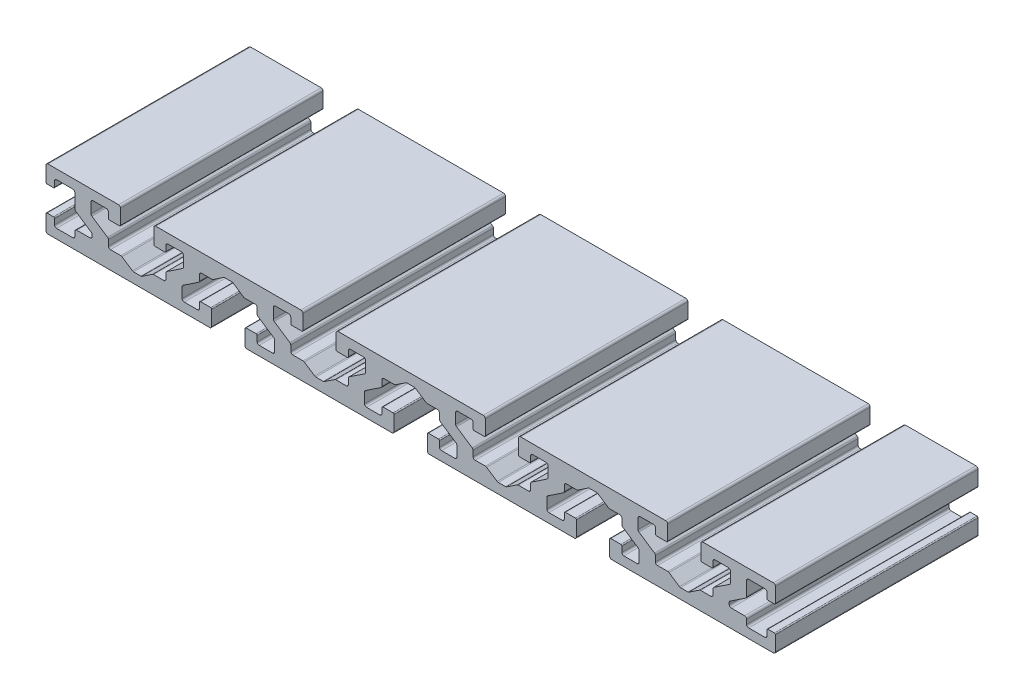
SolidWorks part; units mm, degrees
material "6063-T5"
ref_plane "Front Plane" through (0, 0, 0) normal (0, 0, 1) x (1, 0, 0)
ref_plane "Top Plane" through (0, 0, 0) normal (0, 1, 0) x (1, 0, 0)
ref_plane "Right Plane" through (0, 0, 0) normal (1, 0, 0) x (0, 0, -1)
sketch "Sketch1" plane through (0, 0, 0) normal (0, 0, 1) x (1, 0, 0)
  line L0 (0.5, 0) -> (40.4, 0)
  line L1 (180, 0.5) -> (180, 4.15)
  line L2 (179.5, 15) -> (162.1, 15)
  line L3 (0, 14.5) -> (0, 10.85)
  line L4 (179.75, 4.4) -> (178.15, 4.4)
  line L5 (0.25, 4.4) -> (1.85, 4.4)
  line L6 (179.75, 10.6) -> (178.15, 10.6)
  line L7 (0.25, 10.6) -> (1.85, 10.6)
  line L8 (0, 4.15) -> (0, 0.5)
  line L9 (180, 10.85) -> (180, 14.5)
  line L10 (71.6, 14.5) -> (71.6, 10.85)
  line L11 (18.4, 14.5) -> (18.4, 10.85)
  line L12 (26.6, 14.5) -> (26.6, 10.85)
  line L13 (17.9, 15) -> (0.5, 15)
  line L14 (63.4, 14.5) -> (63.4, 10.85)
  line L15 (116.6, 14.5) -> (116.6, 10.85)
  line L16 (108.4, 14.5) -> (108.4, 10.85)
  line L17 (161.6, 14.5) -> (161.6, 10.85)
  line L18 (153.4, 14.5) -> (153.4, 10.85)
  line L19 (62.9, 15) -> (27.1, 15)
  line L20 (107.9, 15) -> (72.1, 15)
  line L21 (152.9, 15) -> (117.1, 15)
  line L22 (85.9, 0.5) -> (85.9, 4.15)
  line L23 (40.9, 0.5) -> (40.9, 4.15)
  line L24 (49.1, 0.5) -> (49.1, 4.15)
  line L25 (49.6, 0) -> (85.4, 0)
  line L26 (94.1, 0.5) -> (94.1, 4.15)
  line L27 (130.9, 0.5) -> (130.9, 4.15)
  line L28 (139.1, 0.5) -> (139.1, 4.15)
  line L29 (94.6, 0) -> (130.4, 0)
  line L30 (139.6, 0) -> (179.5, 0)
  line L31 (63.15, 10.6) -> (60.65, 10.6)
  line L32 (26.85, 10.6) -> (29.35, 10.6)
  line L33 (18.15, 10.6) -> (15.65, 10.6)
  line L34 (71.85, 10.6) -> (74.35, 10.6)
  line L35 (108.15, 10.6) -> (105.65, 10.6)
  line L36 (116.85, 10.6) -> (119.35, 10.6)
  line L37 (153.15, 10.6) -> (150.65, 10.6)
  line L38 (161.85, 10.6) -> (164.35, 10.6)
  line L39 (40.65, 4.4) -> (38.15, 4.4)
  line L40 (49.35, 4.4) -> (51.85, 4.4)
  line L41 (85.65, 4.4) -> (83.15, 4.4)
  line L42 (94.35, 4.4) -> (96.85, 4.4)
  line L43 (130.65, 4.4) -> (128.15, 4.4)
  line L44 (139.35, 4.4) -> (141.85, 4.4)
  line L45 (52.6, 2.3) -> (55.9, 2.3)
  line L46 (2.6, 2.3) -> (6.6, 2.3)
  line L47 (7.1, 12.2) -> (7.1, 8.7315)
  line L48 (172.9, 12.2) -> (172.9, 8.7315)
  line L49 (6.6, 12.7) -> (2.6, 12.7)
  line L50 (15.4, 10.85) -> (15.4, 12.2)
  line L51 (29.6, 10.85) -> (29.6, 12.2)
  line L52 (74.6, 10.85) -> (74.6, 12.2)
  line L53 (60.4, 10.85) -> (60.4, 12.2)
  line L54 (119.6, 10.85) -> (119.6, 12.2)
  line L55 (105.4, 10.85) -> (105.4, 12.2)
  line L56 (164.6, 10.85) -> (164.6, 12.2)
  line L57 (150.4, 10.85) -> (150.4, 12.2)
  line L58 (37.9, 4.15) -> (37.9, 2.8)
  line L59 (52.1, 4.15) -> (52.1, 2.8)
  line L60 (97.1, 4.15) -> (97.1, 2.8)
  line L61 (82.9, 4.15) -> (82.9, 2.8)
  line L62 (142.1, 4.15) -> (142.1, 2.8)
  line L63 (127.9, 4.15) -> (127.9, 2.8)
  line L64 (56.1, 12.2) -> (56.1, 9.6704)
  line L65 (78.9, 12.2) -> (78.9, 9.6704)
  line L66 (33.9, 12.2) -> (33.9, 9.6704)
  line L67 (30.1, 12.7) -> (33.4, 12.7)
  line L68 (123.6774, 9.2543) -> (119.8226, 6.6845)
  line L69 (21.6056, 2.5) -> (23.3944, 2.5)
  line L70 (11.6, 12.7) -> (14.9, 12.7)
  line L71 (75.1, 12.7) -> (78.4, 12.7)
  line L72 (56.6, 12.7) -> (59.9, 12.7)
  line L73 (120.1, 12.7) -> (123.4, 12.7)
  line L74 (101.6, 12.7) -> (104.9, 12.7)
  line L75 (165.1, 12.7) -> (168.4, 12.7)
  line L76 (146.6, 12.7) -> (149.9, 12.7)
  line L77 (66.6056, 2.5) -> (68.3944, 2.5)
  line L78 (56.3226, 9.2543) -> (60.1774, 6.6845)
  line L79 (101.1, 12.2) -> (101.1, 9.6704)
  line L80 (37.4, 2.3) -> (34.1, 2.3)
  line L81 (97.6, 2.3) -> (100.9, 2.3)
  line L82 (82.4, 2.3) -> (79.1, 2.3)
  line L83 (142.6, 2.3) -> (145.9, 2.3)
  line L84 (127.4, 2.3) -> (124.1, 2.3)
  line L85 (33.6, 2.8) -> (33.6, 5.3296)
  line L86 (56.4, 2.8) -> (56.4, 5.3296)
  line L87 (101.4, 2.8) -> (101.4, 5.3296)
  line L88 (91.1718, 12.416) -> (93.7699, 10.684)
  line L89 (89.1056, 12.5) -> (90.8944, 12.5)
  line L90 (78.8226, 5.7457) -> (82.6774, 8.3155)
  line L91 (168.6774, 9.2543) -> (164.8226, 6.6845)
  line L92 (29.6, 4.9) -> (29.6, 6.2685)
  line L93 (18.4528, 4.4) -> (15.9, 4.4)
  line L94 (26.5472, 4.4) -> (29.1, 4.4)
  line L95 (123.9, 12.2) -> (123.9, 9.6704)
  line L96 (7.3226, 8.3155) -> (11.1774, 5.7457)
  line L97 (15.4, 4.9) -> (15.4, 6.2685)
  line L98 (18.7301, 4.316) -> (21.3282, 2.584)
  line L99 (2.1, 4.15) -> (2.1, 2.8)
  line L100 (2.1, 12.2) -> (2.1, 10.85)
  line L101 (173.4, 12.7) -> (177.4, 12.7)
  line L102 (177.9, 12.2) -> (177.9, 10.85)
  line L103 (173.4, 2.3) -> (177.4, 2.3)
  line L104 (177.9, 2.8) -> (177.9, 4.15)
  line L105 (26.2699, 4.316) -> (23.6718, 2.584)
  line L106 (44.1056, 12.5) -> (45.8944, 12.5)
  line L107 (33.6774, 9.2543) -> (29.8226, 6.6845)
  line L108 (111.6056, 2.5) -> (113.3944, 2.5)
  line L109 (101.3226, 9.2543) -> (105.1774, 6.6845)
  line L110 (146.1, 12.2) -> (146.1, 9.6704)
  line L111 (168.9, 12.2) -> (168.9, 9.6704)
  line L112 (74.6, 4.9) -> (74.6, 6.2685)
  line L113 (156.6056, 2.5) -> (158.3944, 2.5)
  line L114 (97.1, 10.1) -> (97.1, 8.7315)
  line L115 (11.1, 12.2) -> (11.1, 9.6704)
  line L116 (11.3226, 9.2543) -> (15.1774, 6.6845)
  line L117 (146.3226, 9.2543) -> (150.1774, 6.6845)
  line L118 (78.6, 2.8) -> (78.6, 5.3296)
  line L119 (146.4, 2.8) -> (146.4, 5.3296)
  line L120 (33.8226, 5.7457) -> (37.6774, 8.3155)
  line L121 (136.1718, 12.416) -> (138.7699, 10.684)
  line L122 (134.1056, 12.5) -> (135.8944, 12.5)
  line L123 (46.1718, 12.416) -> (48.7699, 10.684)
  line L124 (123.8226, 5.7457) -> (127.6774, 8.3155)
  line L125 (123.6, 2.8) -> (123.6, 5.3296)
  line L126 (78.6774, 9.2543) -> (74.8226, 6.6845)
  line L127 (71.5472, 4.4) -> (74.1, 4.4)
  line L128 (63.4528, 4.4) -> (60.9, 4.4)
  line L129 (60.4, 4.9) -> (60.4, 6.2685)
  line L130 (119.6, 4.9) -> (119.6, 6.2685)
  line L131 (116.5472, 4.4) -> (119.1, 4.4)
  line L132 (108.4528, 4.4) -> (105.9, 4.4)
  line L133 (105.4, 4.9) -> (105.4, 6.2685)
  line L134 (164.6, 4.9) -> (164.6, 6.2685)
  line L135 (161.5472, 4.4) -> (164.1, 4.4)
  line L136 (153.4528, 4.4) -> (150.9, 4.4)
  line L137 (150.4, 4.9) -> (150.4, 6.2685)
  line L138 (63.7301, 4.316) -> (66.3282, 2.584)
  line L139 (71.2699, 4.316) -> (68.6718, 2.584)
  line L140 (108.7301, 4.316) -> (111.3282, 2.584)
  line L141 (116.2699, 4.316) -> (113.6718, 2.584)
  line L142 (153.7301, 4.316) -> (156.3282, 2.584)
  line L143 (161.2699, 4.316) -> (158.6718, 2.584)
  line L144 (11.4, 4.9) -> (11.4, 5.3296)
  line L145 (49.0472, 10.6) -> (51.6, 10.6)
  line L146 (40.9528, 10.6) -> (38.4, 10.6)
  line L147 (37.9, 10.1) -> (37.9, 8.7315)
  line L148 (52.1, 10.1) -> (52.1, 8.7315)
  line L149 (41.2301, 10.684) -> (43.8282, 12.416)
  line L150 (52.3226, 8.3155) -> (56.1774, 5.7457)
  line L151 (94.0472, 10.6) -> (96.6, 10.6)
  line L152 (85.9528, 10.6) -> (83.4, 10.6)
  line L153 (82.9, 10.1) -> (82.9, 8.7315)
  line L154 (142.1, 10.1) -> (142.1, 8.7315)
  line L155 (139.0472, 10.6) -> (141.6, 10.6)
  line L156 (130.9528, 10.6) -> (128.4, 10.6)
  line L157 (127.9, 10.1) -> (127.9, 8.7315)
  line L158 (86.2301, 10.684) -> (88.8282, 12.416)
  line L159 (97.3226, 8.3155) -> (101.1774, 5.7457)
  line L160 (131.2301, 10.684) -> (133.8282, 12.416)
  line L161 (142.3226, 8.3155) -> (146.1774, 5.7457)
  line L162 (7.6, 4.4) -> (10.9, 4.4)
  line L163 (7.1, 3.9) -> (7.1, 2.8)
  line L164 (7.1, 2.3) -> (11.4, 2.3) [skipped]
  line L166 (168.8226, 5.7457) -> (172.6774, 8.3155)
  line L167 (168.6, 4.9) -> (168.6, 5.3296)
  line L170 (172.4, 4.4) -> (169.1, 4.4)
  line L171 (172.9, 3.9) -> (172.9, 2.8)
  line L172 (172.9, 2.3) -> (168.6, 2.3) [skipped]
  line L173 (7.1, 3.9) -> (7.1, 2.3) [skipped]
  line L174 (172.9, 3.9) -> (172.9, 2.3) [skipped]
  arc A0 (0.5, 0) -> (0, 0.5) centre (0.5, 0.5) cw
  arc A1 (0.5, 15) -> (0, 14.5) centre (0.5, 14.5) ccw
  arc A2 (179.5, 0) -> (180, 0.5) centre (179.5, 0.5) ccw
  arc A3 (180, 14.5) -> (179.5, 15) centre (179.5, 14.5) ccw
  arc A4 (161.6, 14.5) -> (162.1, 15) centre (162.1, 14.5) cw
  arc A5 (153.4, 14.5) -> (152.9, 15) centre (152.9, 14.5) ccw
  arc A6 (139.1, 0.5) -> (139.6, 0) centre (139.6, 0.5) ccw
  arc A7 (130.9, 0.5) -> (130.4, 0) centre (130.4, 0.5) cw
  arc A8 (108.4, 14.5) -> (107.9, 15) centre (107.9, 14.5) ccw
  arc A9 (116.6, 14.5) -> (117.1, 15) centre (117.1, 14.5) cw
  arc A10 (85.9, 0.5) -> (85.4, 0) centre (85.4, 0.5) cw
  arc A11 (94.1, 0.5) -> (94.6, 0) centre (94.6, 0.5) ccw
  arc A12 (71.6, 14.5) -> (72.1, 15) centre (72.1, 14.5) cw
  arc A13 (63.4, 14.5) -> (62.9, 15) centre (62.9, 14.5) ccw
  arc A14 (49.6, 0) -> (49.1, 0.5) centre (49.6, 0.5) cw
  arc A15 (40.4, 0) -> (40.9, 0.5) centre (40.4, 0.5) ccw
  arc A16 (17.9, 15) -> (18.4, 14.5) centre (17.9, 14.5) cw
  arc A17 (27.1, 15) -> (26.6, 14.5) centre (27.1, 14.5) ccw
  arc A18 (7.1, 3.9) -> (7.6, 4.4) centre (7.6, 3.9) cw
  arc A19 (10.9, 4.4) -> (11.4, 4.9) centre (10.9, 4.9) ccw
  arc A20 (11.1774, 5.7457) -> (11.4, 5.3296) centre (10.9, 5.3296) cw
  arc A21 (7.3226, 8.3155) -> (7.1, 8.7315) centre (7.6, 8.7315) cw
  arc A22 (2.1, 2.8) -> (2.6, 2.3) centre (2.6, 2.8) ccw
  arc A23 (7.1, 2.8) -> (6.6, 2.3) centre (6.6, 2.8) cw
  arc A24 (7.1, 12.2) -> (6.6, 12.7) centre (6.6, 12.2) ccw
  arc A25 (2.6, 12.7) -> (2.1, 12.2) centre (2.6, 12.2) ccw
  arc A26 (29.6, 12.2) -> (30.1, 12.7) centre (30.1, 12.2) cw
  arc A27 (33.4, 12.7) -> (33.9, 12.2) centre (33.4, 12.2) cw
  arc A28 (33.9, 9.6704) -> (33.6774, 9.2543) centre (33.4, 9.6704) cw
  arc A29 (29.6, 6.2685) -> (29.8226, 6.6845) centre (30.1, 6.2685) cw
  arc A30 (29.1, 4.4) -> (29.6, 4.9) centre (29.1, 4.9) ccw
  arc A31 (26.5472, 4.4) -> (26.2699, 4.316) centre (26.5472, 3.9) ccw
  arc A32 (23.3944, 2.5) -> (23.6718, 2.584) centre (23.3944, 3) ccw
  arc A33 (21.6056, 2.5) -> (21.3282, 2.584) centre (21.6056, 3) cw
  arc A34 (18.4528, 4.4) -> (18.7301, 4.316) centre (18.4528, 3.9) cw
  arc A35 (15.9, 4.4) -> (15.4, 4.9) centre (15.9, 4.9) cw
  arc A36 (15.4, 6.2685) -> (15.1774, 6.6845) centre (14.9, 6.2685) ccw
  arc A37 (11.1, 9.6704) -> (11.3226, 9.2543) centre (11.6, 9.6704) ccw
  arc A38 (11.6, 12.7) -> (11.1, 12.2) centre (11.6, 12.2) ccw
  arc A39 (14.9, 12.7) -> (15.4, 12.2) centre (14.9, 12.2) cw
  arc A40 (52.1, 2.8) -> (52.6, 2.3) centre (52.6, 2.8) ccw
  arc A41 (55.9, 2.3) -> (56.4, 2.8) centre (55.9, 2.8) ccw
  arc A42 (56.4, 5.3296) -> (56.1774, 5.7457) centre (55.9, 5.3296) ccw
  arc A43 (52.1, 8.7315) -> (52.3226, 8.3155) centre (52.6, 8.7315) ccw
  arc A44 (51.6, 10.6) -> (52.1, 10.1) centre (51.6, 10.1) cw
  arc A45 (48.7699, 10.684) -> (49.0472, 10.6) centre (49.0472, 11.1) ccw
  arc A46 (45.8944, 12.5) -> (46.1718, 12.416) centre (45.8944, 12) cw
  arc A47 (44.1056, 12.5) -> (43.8282, 12.416) centre (44.1056, 12) ccw
  arc A48 (41.2301, 10.684) -> (40.9528, 10.6) centre (40.9528, 11.1) cw
  arc A49 (38.4, 10.6) -> (37.9, 10.1) centre (38.4, 10.1) ccw
  arc A50 (37.9, 8.7315) -> (37.6774, 8.3155) centre (37.4, 8.7315) cw
  arc A51 (33.6, 5.3296) -> (33.8226, 5.7457) centre (34.1, 5.3296) cw
  arc A52 (34.1, 2.3) -> (33.6, 2.8) centre (34.1, 2.8) cw
  arc A53 (37.9, 2.8) -> (37.4, 2.3) centre (37.4, 2.8) cw
  arc A54 (60.4, 6.2685) -> (60.1774, 6.6845) centre (59.9, 6.2685) ccw
  arc A55 (60.9, 4.4) -> (60.4, 4.9) centre (60.9, 4.9) cw
  arc A56 (63.4528, 4.4) -> (63.7301, 4.316) centre (63.4528, 3.9) cw
  arc A57 (66.6056, 2.5) -> (66.3282, 2.584) centre (66.6056, 3) cw
  arc A58 (68.6718, 2.584) -> (68.3944, 2.5) centre (68.3944, 3) cw
  arc A59 (71.5472, 4.4) -> (71.2699, 4.316) centre (71.5472, 3.9) ccw
  arc A60 (74.6, 4.9) -> (74.1, 4.4) centre (74.1, 4.9) cw
  arc A61 (74.6, 6.2685) -> (74.8226, 6.6845) centre (75.1, 6.2685) cw
  arc A62 (78.9, 9.6704) -> (78.6774, 9.2543) centre (78.4, 9.6704) cw
  arc A63 (78.9, 12.2) -> (78.4, 12.7) centre (78.4, 12.2) ccw
  arc A64 (74.6, 12.2) -> (75.1, 12.7) centre (75.1, 12.2) cw
  arc A65 (56.1, 9.6704) -> (56.3226, 9.2543) centre (56.6, 9.6704) ccw
  arc A66 (56.1, 12.2) -> (56.6, 12.7) centre (56.6, 12.2) cw
  arc A67 (60.4, 12.2) -> (59.9, 12.7) centre (59.9, 12.2) ccw
  arc A68 (119.6, 12.2) -> (120.1, 12.7) centre (120.1, 12.2) cw
  arc A69 (123.4, 12.7) -> (123.9, 12.2) centre (123.4, 12.2) cw
  arc A70 (123.9, 9.6704) -> (123.6774, 9.2543) centre (123.4, 9.6704) cw
  arc A71 (119.6, 6.2685) -> (119.8226, 6.6845) centre (120.1, 6.2685) cw
  arc A72 (119.6, 4.9) -> (119.1, 4.4) centre (119.1, 4.9) cw
  arc A73 (116.5472, 4.4) -> (116.2699, 4.316) centre (116.5472, 3.9) ccw
  arc A74 (113.6718, 2.584) -> (113.3944, 2.5) centre (113.3944, 3) cw
  arc A75 (111.6056, 2.5) -> (111.3282, 2.584) centre (111.6056, 3) cw
  arc A76 (108.4528, 4.4) -> (108.7301, 4.316) centre (108.4528, 3.9) cw
  arc A77 (105.9, 4.4) -> (105.4, 4.9) centre (105.9, 4.9) cw
  arc A78 (105.4, 6.2685) -> (105.1774, 6.6845) centre (104.9, 6.2685) ccw
  arc A79 (101.1, 9.6704) -> (101.3226, 9.2543) centre (101.6, 9.6704) ccw
  arc A80 (101.6, 12.7) -> (101.1, 12.2) centre (101.6, 12.2) ccw
  arc A81 (105.4, 12.2) -> (104.9, 12.7) centre (104.9, 12.2) ccw
  arc A82 (82.9, 8.7315) -> (82.6774, 8.3155) centre (82.4, 8.7315) cw
  arc A83 (78.8226, 5.7457) -> (78.6, 5.3296) centre (79.1, 5.3296) ccw
  arc A84 (78.6, 2.8) -> (79.1, 2.3) centre (79.1, 2.8) ccw
  arc A85 (82.9, 2.8) -> (82.4, 2.3) centre (82.4, 2.8) cw
  arc A86 (97.1, 2.8) -> (97.6, 2.3) centre (97.6, 2.8) ccw
  arc A87 (101.4, 2.8) -> (100.9, 2.3) centre (100.9, 2.8) cw
  arc A88 (101.4, 5.3296) -> (101.1774, 5.7457) centre (100.9, 5.3296) ccw
  arc A89 (97.1, 8.7315) -> (97.3226, 8.3155) centre (97.6, 8.7315) ccw
  arc A90 (97.1, 10.1) -> (96.6, 10.6) centre (96.6, 10.1) ccw
  arc A91 (94.0472, 10.6) -> (93.7699, 10.684) centre (94.0472, 11.1) cw
  arc A92 (91.1718, 12.416) -> (90.8944, 12.5) centre (90.8944, 12) ccw
  arc A93 (89.1056, 12.5) -> (88.8282, 12.416) centre (89.1056, 12) ccw
  arc A94 (85.9528, 10.6) -> (86.2301, 10.684) centre (85.9528, 11.1) ccw
  arc A95 (83.4, 10.6) -> (82.9, 10.1) centre (83.4, 10.1) ccw
  arc A96 (164.6, 12.2) -> (165.1, 12.7) centre (165.1, 12.2) cw
  arc A97 (168.4, 12.7) -> (168.9, 12.2) centre (168.4, 12.2) cw
  arc A98 (168.9, 9.6704) -> (168.6774, 9.2543) centre (168.4, 9.6704) cw
  arc A99 (164.6, 6.2685) -> (164.8226, 6.6845) centre (165.1, 6.2685) cw
  arc A100 (164.6, 4.9) -> (164.1, 4.4) centre (164.1, 4.9) cw
  arc A101 (161.5472, 4.4) -> (161.2699, 4.316) centre (161.5472, 3.9) ccw
  arc A102 (158.6718, 2.584) -> (158.3944, 2.5) centre (158.3944, 3) cw
  arc A103 (156.6056, 2.5) -> (156.3282, 2.584) centre (156.6056, 3) cw
  arc A104 (153.4528, 4.4) -> (153.7301, 4.316) centre (153.4528, 3.9) cw
  arc A105 (150.9, 4.4) -> (150.4, 4.9) centre (150.9, 4.9) cw
  arc A106 (150.4, 6.2685) -> (150.1774, 6.6845) centre (149.9, 6.2685) ccw
  arc A107 (146.1, 9.6704) -> (146.3226, 9.2543) centre (146.6, 9.6704) ccw
  arc A108 (146.6, 12.7) -> (146.1, 12.2) centre (146.6, 12.2) ccw
  arc A109 (150.4, 12.2) -> (149.9, 12.7) centre (149.9, 12.2) ccw
  arc A110 (142.1, 2.8) -> (142.6, 2.3) centre (142.6, 2.8) ccw
  arc A111 (145.9, 2.3) -> (146.4, 2.8) centre (145.9, 2.8) ccw
  arc A112 (146.4, 5.3296) -> (146.1774, 5.7457) centre (145.9, 5.3296) ccw
  arc A113 (142.1, 8.7315) -> (142.3226, 8.3155) centre (142.6, 8.7315) ccw
  arc A114 (142.1, 10.1) -> (141.6, 10.6) centre (141.6, 10.1) ccw
  arc A115 (139.0472, 10.6) -> (138.7699, 10.684) centre (139.0472, 11.1) cw
  arc A116 (136.1718, 12.416) -> (135.8944, 12.5) centre (135.8944, 12) ccw
  arc A117 (134.1056, 12.5) -> (133.8282, 12.416) centre (134.1056, 12) ccw
  arc A118 (130.9528, 10.6) -> (131.2301, 10.684) centre (130.9528, 11.1) ccw
  arc A119 (128.4, 10.6) -> (127.9, 10.1) centre (128.4, 10.1) ccw
  arc A120 (127.9, 8.7315) -> (127.6774, 8.3155) centre (127.4, 8.7315) cw
  arc A121 (123.8226, 5.7457) -> (123.6, 5.3296) centre (124.1, 5.3296) ccw
  arc A122 (124.1, 2.3) -> (123.6, 2.8) centre (124.1, 2.8) cw
  arc A123 (127.9, 2.8) -> (127.4, 2.3) centre (127.4, 2.8) cw
  arc A124 (172.6774, 8.3155) -> (172.9, 8.7315) centre (172.4, 8.7315) ccw
  arc A125 (168.8226, 5.7457) -> (168.6, 5.3296) centre (169.1, 5.3296) ccw
  arc A126 (169.1, 4.4) -> (168.6, 4.9) centre (169.1, 4.9) cw
  arc A127 (172.9, 3.9) -> (172.4, 4.4) centre (172.4, 3.9) ccw
  arc A128 (172.9, 2.8) -> (173.4, 2.3) centre (173.4, 2.8) ccw
  arc A129 (177.4, 2.3) -> (177.9, 2.8) centre (177.4, 2.8) ccw
  arc A130 (172.9, 12.2) -> (173.4, 12.7) centre (173.4, 12.2) cw
  arc A131 (177.4, 12.7) -> (177.9, 12.2) centre (177.4, 12.2) cw
  arc A132 (119.35, 10.6) -> (119.6, 10.85) centre (119.35, 10.85) ccw
  arc A133 (116.6, 10.85) -> (116.85, 10.6) centre (116.85, 10.85) ccw
  arc A134 (108.4, 10.85) -> (108.15, 10.6) centre (108.15, 10.85) cw
  arc A135 (105.65, 10.6) -> (105.4, 10.85) centre (105.65, 10.85) cw
  arc A136 (96.85, 4.4) -> (97.1, 4.15) centre (96.85, 4.15) cw
  arc A137 (94.1, 4.15) -> (94.35, 4.4) centre (94.35, 4.15) cw
  arc A138 (85.65, 4.4) -> (85.9, 4.15) centre (85.65, 4.15) cw
  arc A139 (82.9, 4.15) -> (83.15, 4.4) centre (83.15, 4.15) cw
  arc A140 (74.35, 10.6) -> (74.6, 10.85) centre (74.35, 10.85) ccw
  arc A141 (71.6, 10.85) -> (71.85, 10.6) centre (71.85, 10.85) ccw
  arc A142 (63.4, 10.85) -> (63.15, 10.6) centre (63.15, 10.85) cw
  arc A143 (60.65, 10.6) -> (60.4, 10.85) centre (60.65, 10.85) cw
  arc A144 (51.85, 4.4) -> (52.1, 4.15) centre (51.85, 4.15) cw
  arc A145 (49.1, 4.15) -> (49.35, 4.4) centre (49.35, 4.15) cw
  arc A146 (40.9, 4.15) -> (40.65, 4.4) centre (40.65, 4.15) ccw
  arc A147 (38.15, 4.4) -> (37.9, 4.15) centre (38.15, 4.15) ccw
  arc A148 (29.35, 10.6) -> (29.6, 10.85) centre (29.35, 10.85) ccw
  arc A149 (26.6, 10.85) -> (26.85, 10.6) centre (26.85, 10.85) ccw
  arc A150 (18.4, 10.85) -> (18.15, 10.6) centre (18.15, 10.85) cw
  arc A151 (15.65, 10.6) -> (15.4, 10.85) centre (15.65, 10.85) cw
  arc A152 (0, 4.15) -> (0.25, 4.4) centre (0.25, 4.15) cw
  arc A153 (1.85, 4.4) -> (2.1, 4.15) centre (1.85, 4.15) cw
  arc A154 (1.85, 10.6) -> (2.1, 10.85) centre (1.85, 10.85) ccw
  arc A155 (0, 10.85) -> (0.25, 10.6) centre (0.25, 10.85) ccw
  arc A156 (178.15, 4.4) -> (177.9, 4.15) centre (178.15, 4.15) ccw
  arc A157 (179.75, 4.4) -> (180, 4.15) centre (179.75, 4.15) cw
  arc A158 (179.75, 10.6) -> (180, 10.85) centre (179.75, 10.85) ccw
  arc A159 (178.15, 10.6) -> (177.9, 10.85) centre (178.15, 10.85) cw
  arc A160 (164.35, 10.6) -> (164.6, 10.85) centre (164.35, 10.85) ccw
  arc A161 (161.6, 10.85) -> (161.85, 10.6) centre (161.85, 10.85) ccw
  arc A162 (153.4, 10.85) -> (153.15, 10.6) centre (153.15, 10.85) cw
  arc A163 (150.65, 10.6) -> (150.4, 10.85) centre (150.65, 10.85) cw
  arc A164 (141.85, 4.4) -> (142.1, 4.15) centre (141.85, 4.15) cw
  arc A165 (139.1, 4.15) -> (139.35, 4.4) centre (139.35, 4.15) cw
  arc A166 (130.9, 4.15) -> (130.65, 4.4) centre (130.65, 4.15) ccw
  arc A167 (128.15, 4.4) -> (127.9, 4.15) centre (128.15, 4.15) ccw
  point P228 (7.1, 2.3)
  dimension "D3" = 2
  dimension "D1" = 2
  dimension "D4" = 3
  dimension "D2" = 3
extrude "Boss-Extrude1" add sketch "Sketch1" along normal blind 50 contours L19 A17 L12 A149 L32 A148 L51 A26 L67 A27 L66 A28 L107 A29 L92 A30 L94 A31 L105 A32 L69 A33 L98 A34 L93 A35 L97 A36 L116 A37 L115 A38 L70 A39 L50 A151 L33 A150 L11 A16 L13 A1 L3 A155 L7 A154 L100 A25 L49 A24 L47 A21 L96 A20 L144 A19 L162 A18 L163 A23 L46 A22 L99 A153 L5 A152 L8 A0 L0 A15 L23 A146 L39 A147 L58 A53 L80 A52 L85 A51 L120 A50 L147 A49 L146 A48 L149 A47 L106 A46 L123 A45 L145 A44 L148 A43 L150 A42 L86 A41 L45 A40 L59 A144 L40 A145 L24 A14 L25 A10 L22 A138 L41 A139 L61 A85 L82 A84 L118 A83 L90 A82 L153 A95 L152 A94 L158 A93 L89 A92 L88 A91 L151 A90 L114 A89 L159 A88 L87 A87 L81 A86 L60 A136 L42 A137 L26 A11 L29 A7 L27 A166 L43 A167 L63 A123 L84 A122 L125 A121 L124 A120 L157 A119 L156 A118 L160 A117 L122 A116 L121 A115 L155 A114 L154 A113 L161 A112 L119 A111 L83 A110 L62 A164 L44 A165 L28 A6 L30 A2 L1 A157 L4 A156 L104 A129 L103 A128 L171 A127 L170 A126 L167 A125 L166 A124 L48 A130 L101 A131 L102 A159 L6 A158 L9 A3 L2 A4 L17 A161 L38 A160 L56 A96 L75 A97 L111 A98 L91 A99 L134 A100 L135 A101 L143 A102 L113 A103 L142 A104 L136 A105 L137 A106 L117 A107 L110 A108 L76 A109 L57 A163 L37 A162 L18 A5 L21 A9 L15 A133 L36 A132 L54 A68 L73 A69 L95 A70 L68 A71 L130 A72 L131 A73 L141 A74 L108 A75 L140 A76 L132 A77 L133 A78 L109 A79 L79 A80 L74 A81 L55 A135 L35 A134 L16 A8 L20 A12 L10 A141 L34 A140 L52 A64 L71 A63 L65 A62 L126 A61 L112 A60 L127 A59 L139 A58 L77 A57 L138 A56 L128 A55 L129 A54 L78 A65 L64 A66 L72 A67 L53 A143 L31 A142 L14 A13
